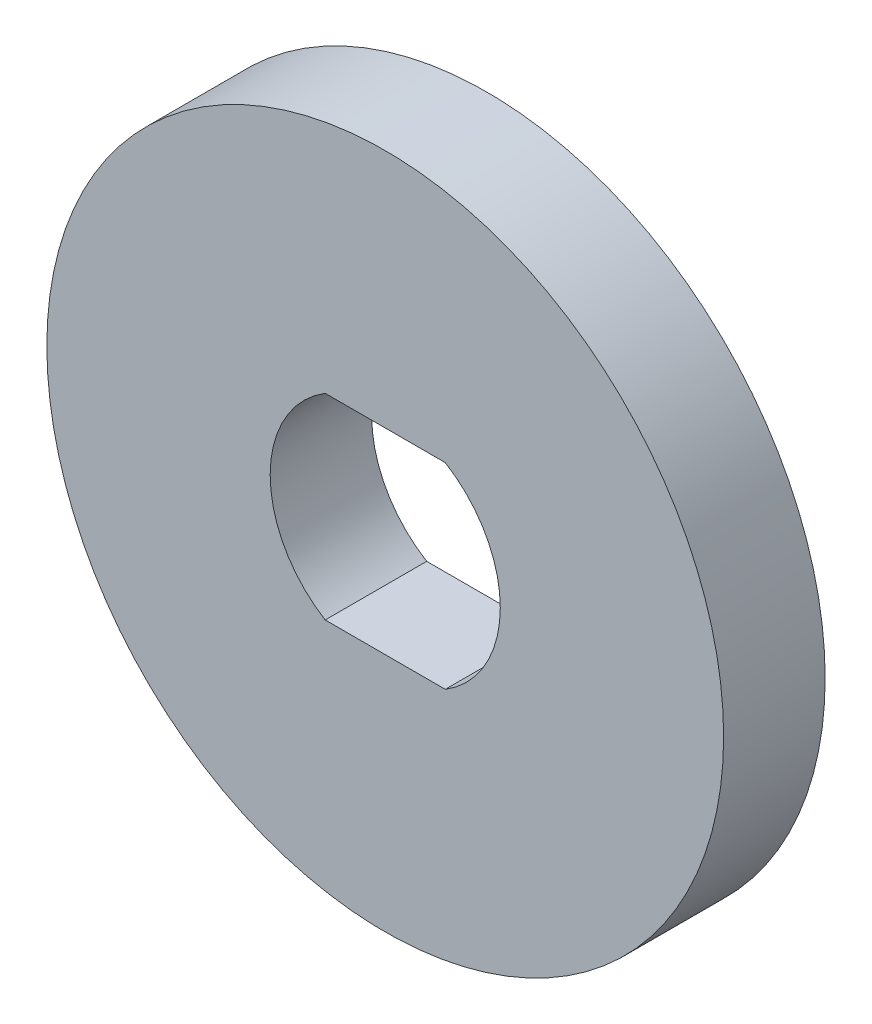
SolidWorks part; units mm, degrees
ref_plane "Front Plane" through (0, 0, 0) normal (0, 0, 1) x (1, 0, 0)
ref_plane "Top Plane" through (0, 0, 0) normal (0, 1, 0) x (1, 0, 0)
ref_plane "Right Plane" through (0, 0, 0) normal (1, 0, 0) x (0, 0, -1)
sketch "Sketch1" plane through (0, 0, 0) normal (0, 0, 1) x (1, 0, 0)
  line L0 (-1.7748, 2.9) -> (1.7748, 2.9)
  line L1 (-1.6583, -2.5) -> (1.6583, -2.5) construction
  line L2 (-1.6583, -2.5) -> (-1.6583, 2.5) construction
  line L3 (-1.6583, 2.5) -> (1.6583, 2.5) construction
  line L4 (1.6583, -2.5) -> (1.6583, 2.5) construction
  line L5 (-1.6583, -2.5) -> (1.6583, 2.5) construction
  line L6 (-1.6583, 2.5) -> (1.6583, -2.5) construction
  line L7 (-1.7748, -2.9) -> (1.7748, -2.9)
  circle A0 centre (0, 0) radius 10
  arc A1 (-1.6583, 2.5) -> (-1.6583, -2.5) centre (0, 0) ccw construction
  arc A2 (1.6583, -2.5) -> (1.6583, 2.5) centre (0, 0) ccw construction
  arc A3 (1.7748, -2.9) -> (1.7748, 2.9) centre (0, 0) ccw
  arc A4 (-1.7748, 2.9) -> (-1.7748, -2.9) centre (0, 0) ccw
  dimension "D1" = 20
  dimension "D2" = 6
  dimension "D3" = 2.5
  dimension "D4" = 0.4
extrude "Boss-Extrude1" add sketch "Sketch1" along normal blind 3
